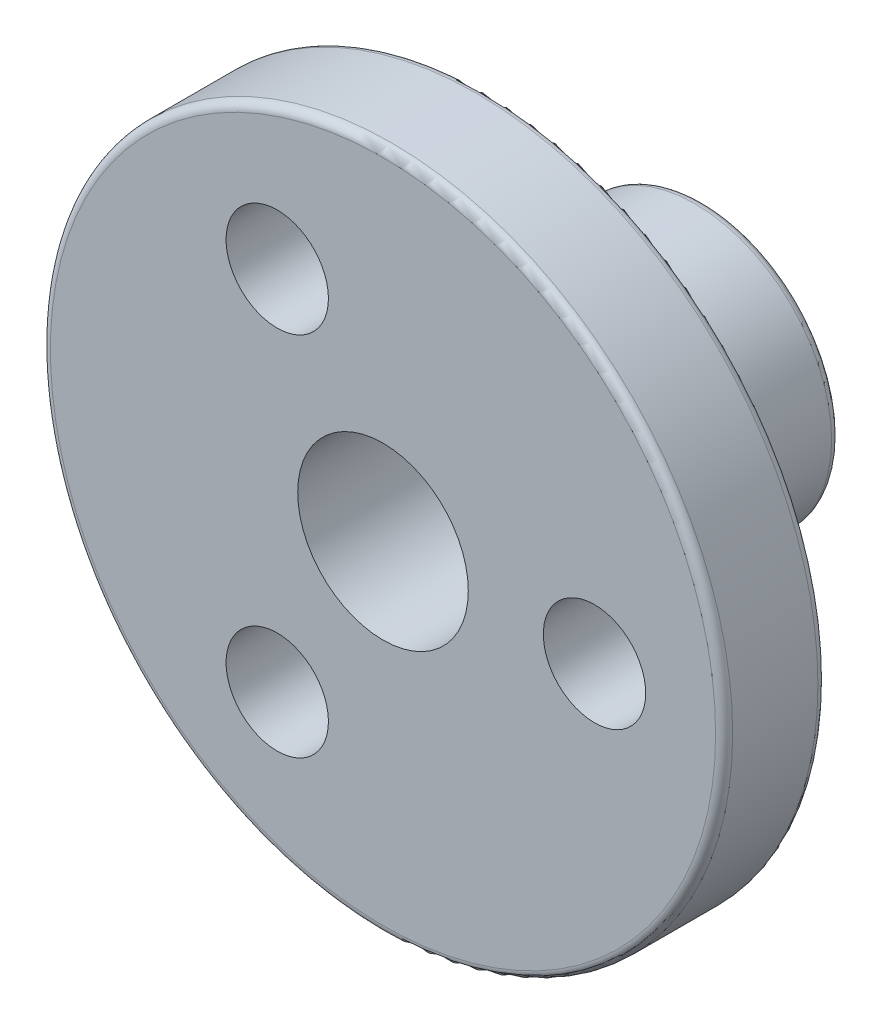
SolidWorks part; units mm, degrees
ref_plane "Front Plane" through (0, 0, 0) normal (0, 0, 1) x (1, 0, 0)
ref_plane "Top Plane" through (0, 0, 0) normal (0, 1, 0) x (1, 0, 0)
ref_plane "Right Plane" through (0, 0, 0) normal (1, 0, 0) x (0, 0, -1)
sketch "Sketch1" plane through (0, 0, 0) normal (0, 0, 1) x (1, 0, 0)
  circle A0 centre (0, 0) radius 10
  circle A1 centre (0, 0) radius 2.5
  circle A2 centre (0, 0) radius 6.2 construction
  circle A3 centre (6.2, 0) radius 1.5
  circle A4 centre (-3.1, -5.3694) radius 1.5
  circle A5 centre (-3.1, 5.3694) radius 1.5
  point P14 (0, 0)
  dimension "D1" = 20
  dimension "D2" = 5
  dimension "D3" = 12.4
  dimension "D4" = 3
  dimension "D5" = 3
extrude "Boss-Extrude1" add sketch "Sketch1" along normal blind 3
sketch "Sketch2" plane through (0, 0, 0) normal (0, 0, -1) x (-1, 0, 0)
  circle A0 centre (0, 0) radius 4
  circle A1 centre (0, 0) radius 2.5
  circle M4 centre (0, 0) radius 2.5
  dimension "D1" = 8
extrude "Boss-Extrude2" add sketch "Sketch2" along normal blind 6.4 contours A0 M4
fillet "Fillet1" radius 0.25 1 edges at (4, 0, 0)
fillet "Fillet2" radius 0.25 1 edges at (-4, 0, -6.4)
fillet "Fillet3" radius 0.25 2 edges at (10, 0, 0) (10, 0, 3)
